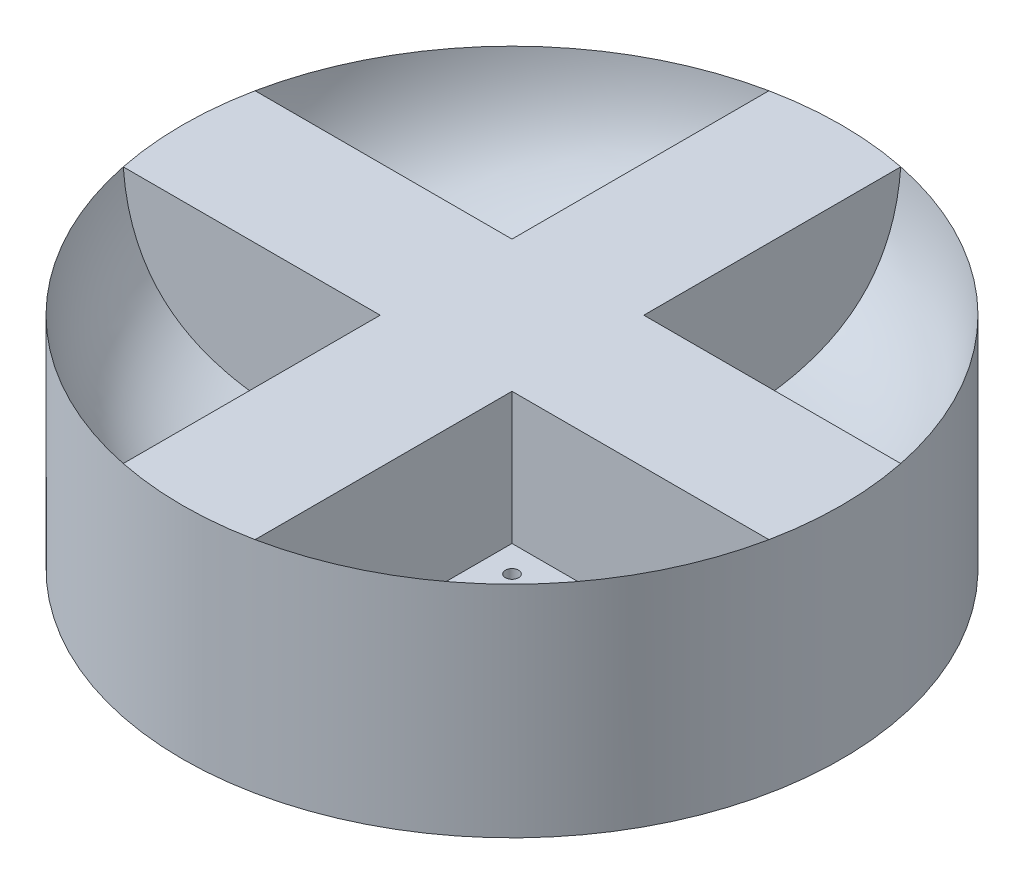
SolidWorks part; units mm, degrees
ref_plane "Front Plane" through (0, 0, 0) normal (0, 0, 1) x (1, 0, 0)
ref_plane "Top Plane" through (0, 0, 0) normal (0, 1, 0) x (1, 0, 0)
ref_plane "Right Plane" through (0, 0, 0) normal (1, 0, 0) x (0, 0, -1)
sketch "Sketch1" plane through (0, 0, 0) normal (0, 1, 0) x (1, 0, 0)
  circle A0 centre (0, 0) radius 37.5
  dimension "D1" = 75
extrude "Boss-Extrude1" add sketch "Sketch1" along normal blind 10
sketch "Sketch5" plane through (0, 0, 0) normal (1, 0, 0) x (0, 0, -1)
  line L0 (0, 0) -> (0, 44.7433) construction
  line L1 (-37.5, 25) -> (-37.5, 10)
  line L2 (-37.5, 0) -> (-37.5, 48.3968) construction
  line L3 (-37.5, 10) -> (-22.5, 10)
  line L5 (37.5, 10) -> (-37.5, 10) construction
  spline S0 degree 2 poles (-37.5, 25) (-36.4684, 11.4052) (-22.5, 10) knots 0 0 0 1 1 1
  dimension "D1" = 15
  dimension "D2" = 5
  dimension "D3" = 15
  dimension "D4" = 7.5
revolve "Revolve1" add sketch "Sketch5" angle 360 about L0
ref_plane "Plane2" through (0, 25, 0) normal (0, 1, 0) x (1, 0, 0)
sketch "Sketch7" plane through (0, 10, 0) normal (0, 1, 0) x (1, 0, 0)
  line L0 (7.5, 7.5) -> (7.5, 36.7423)
  line L1 (7.5, -7.5) -> (36.7423, -7.5)
  line L2 (-7.5, 36.7423) -> (-7.5, 7.5)
  line L3 (-7.5, 7.5) -> (7.5, 7.5) construction
  line L4 (36.7423, 7.5) -> (7.5, 7.5)
  line L5 (-7.5, -7.5) -> (-7.5, -36.7423)
  line L6 (7.5, -36.7423) -> (7.5, -7.5)
  line L7 (-7.5, 7.5) -> (-36.7423, 7.5)
  line L8 (-36.7423, -7.5) -> (-7.5, -7.5)
  circle A0 centre (0, 0) radius 37.5 construction
  arc A1 (-7.5, 36.7423) -> (7.5, 36.7423) centre (0, 0) cw
  arc A2 (36.7423, 7.5) -> (36.7423, -7.5) centre (0, 0) cw
  arc A3 (7.5, -36.7423) -> (-7.5, -36.7423) centre (0, 0) cw
  arc A4 (-36.7423, -7.5) -> (-36.7423, 7.5) centre (0, 0) cw
  point P2 (0, 7.5)
  point P21 (0, 0)
  point P25 (0, 0)
  dimension "D1" = 7.5
  dimension "D2" = 15
extrude "Boss-Extrude2" add sketch "Sketch7" along normal up to surface (15 mm away) up to plane "Plane2"
sketch "Sketch8" plane through (0, 10, 0) normal (0, 1, 0) x (1, 0, 0)
  line L0 (-13.903, 9.5069) -> (-8.6503, 14.7596) construction
  line L1 (-7.5, 7.5) -> (-36.7423, 7.5) construction
  line L2 (-7.5, 7.5) -> (-15.9099, 15.9099) construction
  line L4 (-11.705, 11.705) -> (0, 0) construction
  circle A1 centre (-10.5029, 10.5029) radius 0.75
  circle A10 centre (-12.907, 12.907) radius 0.75
  arc A11 (-7.5, 21.2132) -> (-21.2132, 7.5) centre (0, 0) ccw construction
  circle A12 centre (10.5029, 10.5029) radius 0.75
  circle A13 centre (12.907, 12.907) radius 0.75
  circle A14 centre (10.5029, -10.5029) radius 0.75
  circle A15 centre (12.907, -12.907) radius 0.75
  circle A16 centre (-10.5029, -10.5029) radius 0.75
  circle A17 centre (-12.907, -12.907) radius 0.75
  point P0 (-11.705, 11.705)
  point P30 (0, 0)
  point P37 (0, 0)
  point P38 (-11.705, 11.705)
  dimension "D2" = 4
  dimension "D4" = 1.5
  dimension "D1" = 45
  dimension "D3" = 1.7
extrude "Cut-Extrude1" cut sketch "Sketch8" against normal through all
